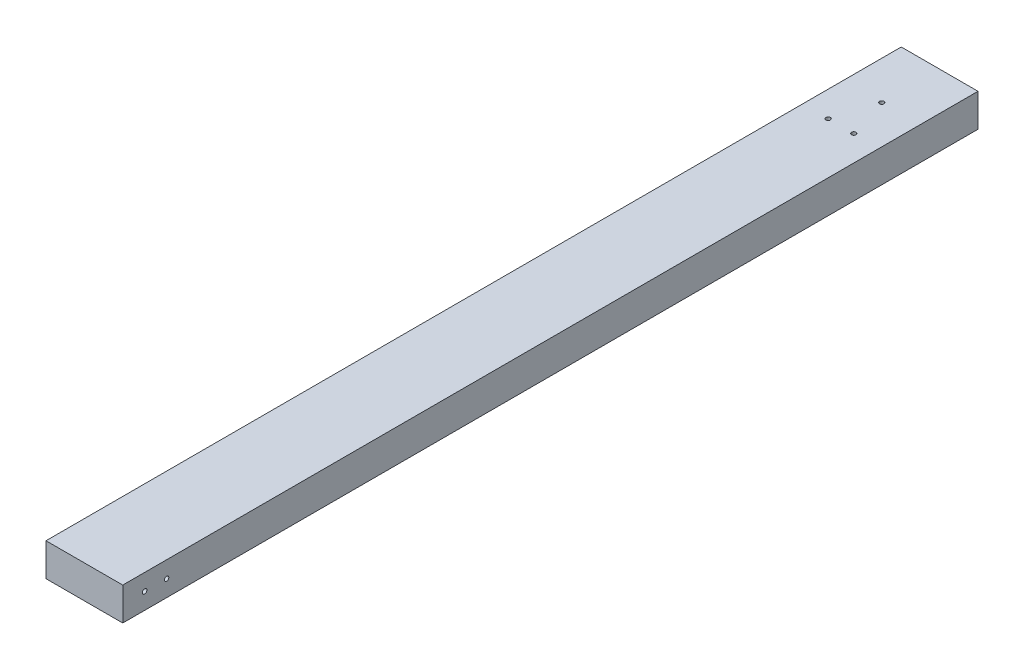
SolidWorks part; units mm, degrees
ref_plane "Front Plane" through (0, 0, 0) normal (0, 0, 1) x (1, 0, 0)
ref_plane "Top Plane" through (0, 0, 0) normal (0, 1, 0) x (1, 0, 0)
ref_plane "Right Plane" through (0, 0, 0) normal (1, 0, 0) x (0, 0, -1)
sketch "Sketch1" plane through (0, 0, 0) normal (0, 0, 1) x (1, 0, 0)
  line L1 (-88.9, 42.177) -> (0, 42.177)
  line L2 (-88.9, 42.177) -> (-88.9, 4.077)
  line L3 (-88.9, 4.077) -> (0, 4.077)
  line L4 (0, 42.177) -> (0, 4.077)
  dimension "D1" = 88.9
  dimension "D2" = 38.1
extrude "Boss-Extrude1" add sketch "Sketch1" along normal blind 990.6
sketch "Sketch2" plane through (-88.9, 0, 0) normal (-1, 0, 0) x (0, 0, 1)
  line L2 (990.6, 42.177) -> (990.6, 4.077) construction
  circle A0 centre (939.8, 23.127) radius 2.5797
  circle A1 centre (965.2, 23.127) radius 2.5797
  point P1 (939.8, 23.127)
  point P2 (965.2, 23.127)
  dimension "D5" = 5.1594
  dimension "D6" = 5.1594
  dimension "D1" = 50.8
  dimension "D2" = 25.4
extrude "Cut-Extrude1" cut sketch "Sketch2" against normal through all
sketch "Sketch3" plane through (0, 4.077, 0) normal (0, -1, 0) x (1, 0, 0)
  line L0 (-88.9, 0) -> (0, 0) construction
  line L1 (0, 990.6) -> (0, 0) construction
  line L2 (-88.9, 990.6) -> (-88.9, 0) construction
  line L3 (-88.9, 990.6) -> (0, 990.6) construction
  circle A0 centre (-44.45, 67.1139) radius 2.5797
  circle A1 centre (-29.6333, 114.3) radius 2.5797
  circle A2 centre (-59.2667, 114.3) radius 2.5797
  point P0 (-44.45, 67.1139)
  dimension "D1" = 5.1594
  dimension "D6" = 5.1594
  dimension "D7" = 5.1594
  dimension "D2" = 114.3
  dimension "D3" = 114.3
  dimension "D4" = 29.6333
  dimension "D5" = 29.6333
  dimension "D8" = 876.3
extrude "Cut-Extrude2" cut sketch "Sketch3" against normal through all
